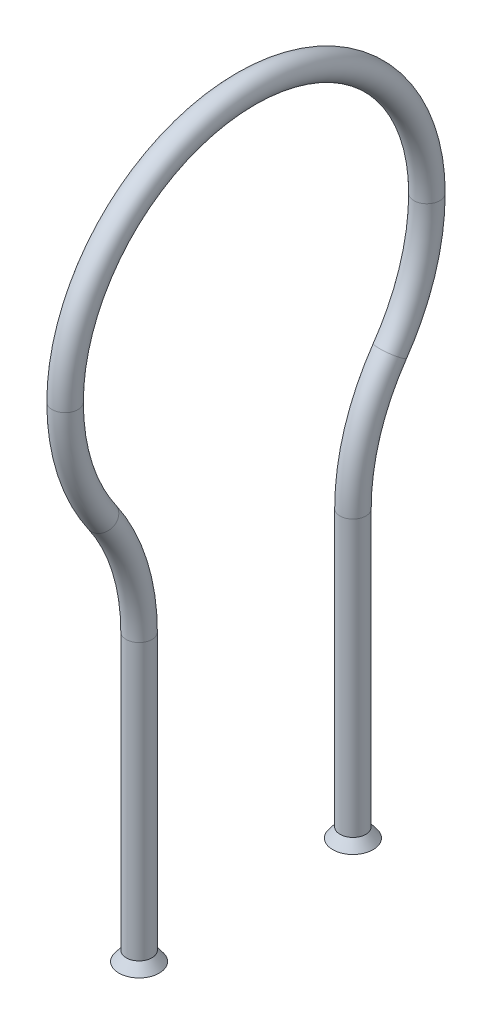
SolidWorks part; units mm, degrees
material "6061-T6 (SS)"
ref_plane "Front Plane" through (0, 0, 0) normal (0, 0, 1) x (1, 0, 0)
ref_plane "Top Plane" through (0, 0, 0) normal (0, 1, 0) x (1, 0, 0)
ref_plane "Right Plane" through (0, 0, 0) normal (1, 0, 0) x (0, 0, -1)
sketch "Sketch8" plane through (0, 0, 0) normal (0, 0, 1) x (1, 0, 0)
  circle A0 centre (0, 0) radius 2.3812
  circle A1 centre (0, 0) radius 1.8224
  dimension "D1" = 0.5588
  dimension "D2" = 4.7625
sketch "Sketch9" plane through (0, 0, 0) normal (1, 0, 0) x (0, 0, -1)
  line L0 (0, 0) -> (0, -33.3375) construction
  line L1 (0, -33.3375) -> (-33.3375, -33.3375) construction
  line L2 (-19.7022, -76.8357) -> (-19.7022, -127.6357)
  arc A0 (0, 0) -> (-33.3375, -33.3375) centre (0, -33.3375) ccw
  arc A1 (-33.3375, -33.3375) -> (-26.5199, -55.0866) centre (4.7625, -33.3375) ccw
  arc A2 (-26.5199, -55.0866) -> (-19.7022, -76.8357) centre (-57.8022, -76.8357) cw
  dimension "D1" = 33.3375
  dimension "D3" = 38.1
  dimension "D4" = 38.1
  dimension "D2" = 50.8
  dimension "D5" = 19.7022
sweep "Sweep2" add profiles "Sketch8" path "Sketch9"
sketch "Sketch10" plane through (0, -127.6357, 0) normal (0, -1, 0) x (1, 0, 0)
  circle A0 centre (0, 19.7022) radius 2.3812 construction
  circle A2 centre (0, 19.7022) radius 2.3813
extrude "Boss-Extrude3" add sketch "Sketch10" along normal blind 1.778 draft 37 draft outward yes
sketch "Sketch11" plane through (0, -127.6357, 0) normal (0, 1, 0) x (1, 0, 0)
  circle A0 centre (0, -19.7022) radius 1.8224 construction
  circle A1 centre (0, -19.7022) radius 1.8225
extrude "Cut-Extrude2" cut sketch "Sketch11" against normal through all draft 37 draft outward yes
mirror "Mirror1" about plane through (0, 0, 0) normal (0, 0, 1) of "Cut-Extrude2", "Boss-Extrude3", "Sweep2"
